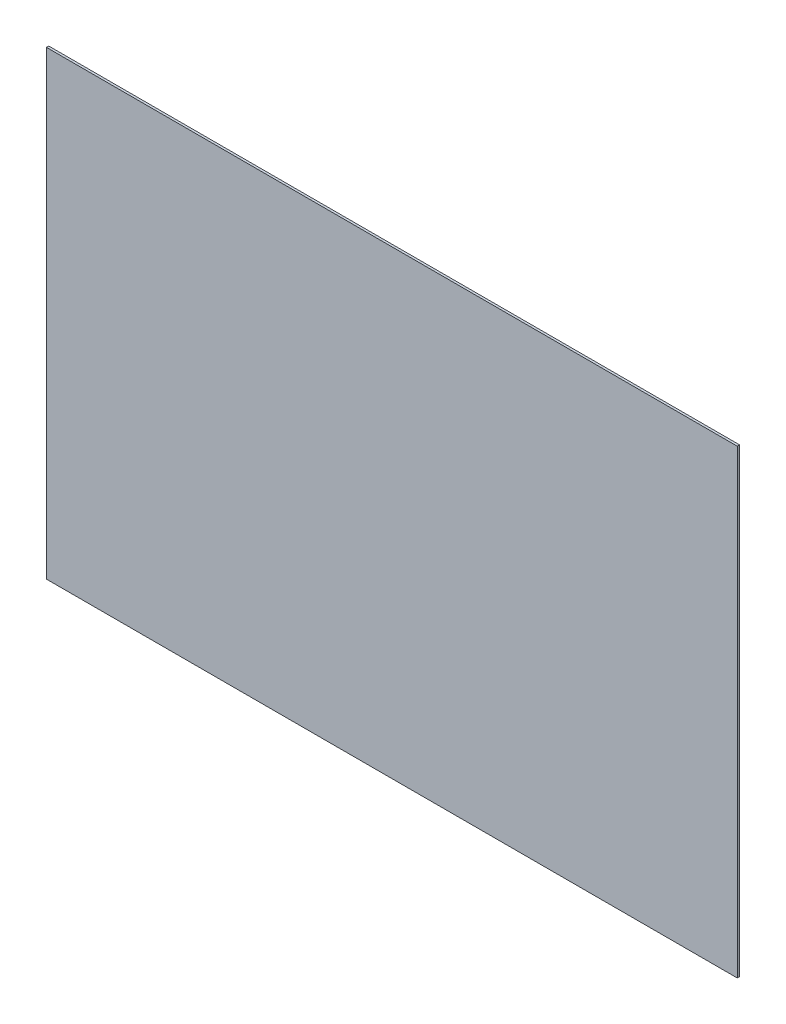
SolidWorks part; units mm, degrees
ref_plane "Front Plane" through (0, 0, 0) normal (0, 0, 1) x (1, 0, 0)
ref_plane "Top Plane" through (0, 0, 0) normal (0, 1, 0) x (1, 0, 0)
ref_plane "Right Plane" through (0, 0, 0) normal (1, 0, 0) x (0, 0, -1)
sketch "Sketch1" plane through (0, 0, 0) normal (0, 0, 1) x (1, 0, 0)
  line L1 (348.5034, 118.4173) -> (48.5034, 118.4173)
  line L2 (348.5034, 118.4173) -> (348.5034, 318.4173)
  line L3 (348.5034, 318.4173) -> (48.5034, 318.4173)
  line L4 (48.5034, 118.4173) -> (48.5034, 318.4173)
  point P4 (348.5034, 318.4173)
  dimension "D1" = 300
  dimension "D2" = 200
extrude "Boss-Extrude1" add sketch "Sketch1" along normal blind 1
